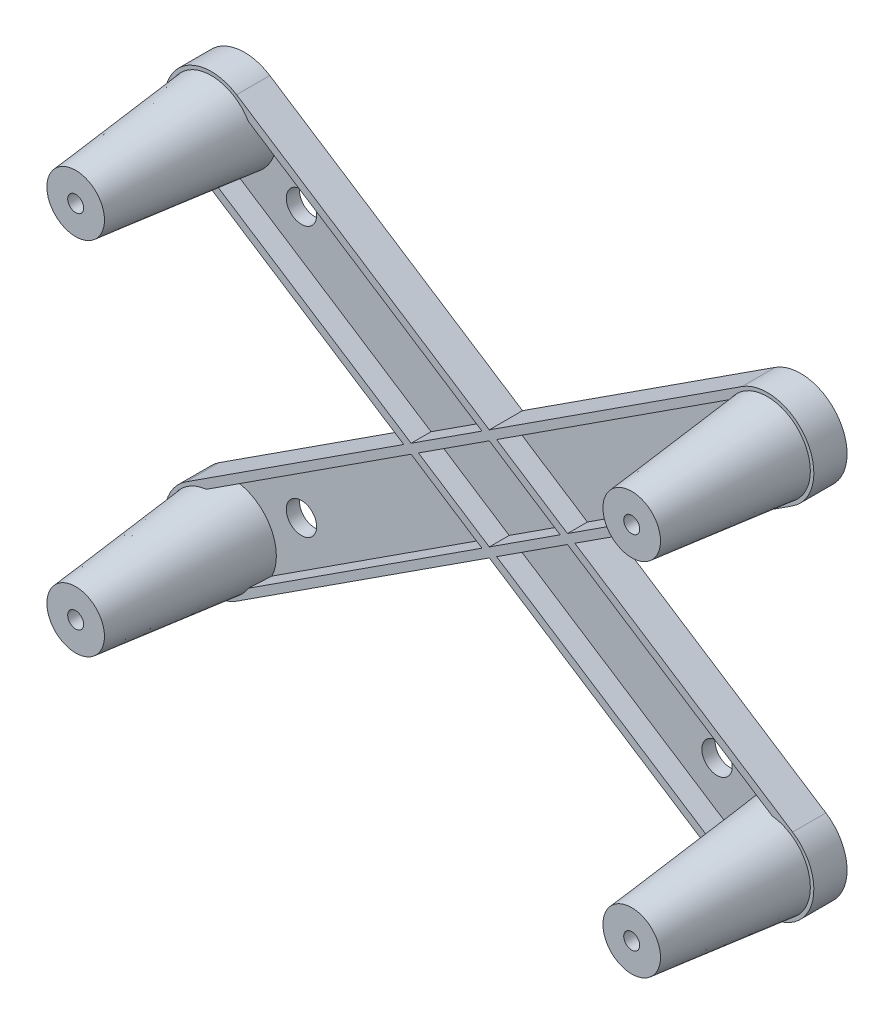
SolidWorks part; units mm, degrees
ref_plane "Front Plane" through (0, 0, 0) normal (0, 0, 1) x (1, 0, 0)
ref_plane "Top Plane" through (0, 0, 0) normal (0, 1, 0) x (1, 0, 0)
ref_plane "Right Plane" through (0, 0, 0) normal (1, 0, 0) x (0, 0, -1)
sketch "Guide Sketch" plane through (0, 0, 0) normal (0, 0, 1) x (1, 0, 0)
  circle A0 centre (0, 0) radius 1.75
  circle A1 centre (83.65, 0) radius 1.75
  circle A2 centre (83.65, 54.24) radius 1.75
  circle A3 centre (0, 54.24) radius 1.75
  dimension "D1" = 3.5
  dimension "D2" = 2
  dimension "D3" = 2
sketch "Sketch2" plane through (0, 0, 0) normal (0, 0, 1) x (1, 0, 0)
  line L0 (0, 54.24) -> (83.65, 0) construction
  line L1 (3.8084, 60.1134) -> (87.4584, 5.8734)
  line L2 (-3.8084, 48.3666) -> (79.8416, -5.8734)
  line L3 (83.65, 54.24) -> (0, 0) construction
  line L4 (87.4584, 48.3666) -> (3.8084, -5.8734)
  line L5 (79.8416, 60.1134) -> (-3.8084, 5.8734)
  line L6 (86.8055, 49.3735) -> (3.1555, -4.8665)
  line L7 (80.4945, 59.1065) -> (-3.1555, 4.8665)
  line L8 (3.1555, 59.1065) -> (86.8055, 4.8665)
  line L9 (-3.1555, 49.3735) -> (80.4945, -4.8665)
  arc A0 (3.8084, 60.1134) -> (-3.8084, 48.3666) centre (0, 54.24) ccw
  arc A1 (79.8416, -5.8734) -> (87.4584, 5.8734) centre (83.65, 0) ccw
  arc A2 (87.4584, 48.3666) -> (79.8416, 60.1134) centre (83.65, 54.24) ccw
  arc A3 (-3.8084, 5.8734) -> (3.8084, -5.8734) centre (0, 0) ccw
  arc A4 (-3.1555, 4.8665) -> (3.1555, -4.8665) centre (0, 0) ccw
  arc A5 (86.8055, 49.3735) -> (80.4945, 59.1065) centre (83.65, 54.24) ccw
  arc A6 (80.4945, -4.8665) -> (86.8055, 4.8665) centre (83.65, 0) ccw
  arc A7 (3.1555, 59.1065) -> (-3.1555, 49.3735) centre (0, 54.24) ccw
  point P4 (41.825, 27.12)
  point P9 (41.825, 27.12)
  dimension "D1" = 7
  dimension "D2" = 1.2
  dimension "D3" = 1.2
extrude "Base" add sketch "Sketch2" along normal blind 2 contours L4 A3 L5 A2 | L2 A1 L1 A0
sketch "Sketch3" plane through (0, 0, 0) normal (0, 0, 1) x (1, 0, 0)
  circle A0 centre (0, 54.24) radius 7
  circle A1 centre (0, 0) radius 7
  circle A2 centre (83.65, 0) radius 7
  circle A3 centre (83.65, 54.24) radius 7
extrude "Mounting Bosses" add sketch "Sketch3" along normal blind 25.4 draft 6
sketch "Sketch5" plane through (0, 0, 0) normal (0, 0, 1) x (1, 0, 0)
  line L0 (79.8416, 60.1134) -> (-3.8084, 5.8734) construction
  line L1 (80.4945, 59.1065) -> (-3.1555, 4.8665) construction
  line L2 (-3.8084, 48.3666) -> (79.8416, -5.8734) construction
  line L3 (-3.1555, 49.3735) -> (80.4945, -4.8665) construction
  line L4 (3.1555, 59.1065) -> (86.8055, 4.8665) construction
  line L5 (86.8055, 49.3735) -> (3.1555, -4.8665) construction
  line L6 (79.8416, 60.1134) -> (41.825, 35.4628)
  line L7 (80.4945, 59.1065) -> (42.9278, 34.7477)
  line L8 (-3.8084, 48.3666) -> (28.9586, 27.12)
  line L9 (-3.1555, 49.3735) -> (30.0615, 27.8351)
  line L10 (3.1555, 59.1065) -> (40.7222, 34.7477)
  line L11 (86.8055, 49.3735) -> (53.5885, 27.8351)
  line L12 (87.4584, 48.3666) -> (3.8084, -5.8734) construction
  line L13 (87.4584, 48.3666) -> (54.6914, 27.12)
  line L14 (30.0615, 26.4049) -> (40.7222, 19.4923)
  line L15 (31.1643, 27.12) -> (41.825, 20.2074)
  line L16 (28.9586, 27.12) -> (-3.8084, 5.8734)
  line L17 (30.0615, 26.4049) -> (-3.1555, 4.8665)
  line L18 (41.825, 18.7772) -> (79.8416, -5.8734)
  line L19 (42.9278, 19.4923) -> (80.4945, -4.8665)
  line L20 (41.825, 18.7772) -> (3.8084, -5.8734)
  line L21 (40.7222, 19.4923) -> (3.1555, -4.8665)
  line L22 (3.8084, 60.1134) -> (87.4584, 5.8734) construction
  line L23 (3.8084, 60.1134) -> (41.825, 35.4628)
  line L24 (41.825, 34.0326) -> (52.4857, 27.12)
  line L25 (42.9278, 34.7477) -> (53.5885, 27.8351)
  line L26 (40.7222, 34.7477) -> (30.0615, 27.8351)
  line L27 (41.825, 34.0326) -> (31.1643, 27.12)
  line L28 (53.5885, 26.4049) -> (42.9278, 19.4923)
  line L29 (52.4857, 27.12) -> (41.825, 20.2074)
  line L30 (53.5885, 26.4049) -> (86.8055, 4.8665)
  line L31 (54.6914, 27.12) -> (87.4584, 5.8734)
  arc A0 (3.1555, 59.1065) -> (-3.1555, 49.3735) centre (0, 54.24) ccw construction
  arc A1 (-3.1555, 4.8665) -> (3.1555, -4.8665) centre (0, 0) ccw construction
  arc A2 (80.4945, -4.8665) -> (86.8055, 4.8665) centre (83.65, 0) ccw construction
  arc A3 (3.1555, 59.1065) -> (-3.1555, 49.3735) centre (0, 54.24) ccw
  arc A4 (-3.1555, 4.8665) -> (3.1555, -4.8665) centre (0, 0) ccw
  arc A5 (80.4945, -4.8665) -> (86.8055, 4.8665) centre (83.65, 0) ccw
  arc A6 (-3.8084, 5.8734) -> (3.8084, -5.8734) centre (0, 0) ccw construction
  arc A7 (3.8084, 60.1134) -> (-3.8084, 48.3666) centre (0, 54.24) ccw construction
  arc A8 (-3.8084, 5.8734) -> (3.8084, -5.8734) centre (0, 0) ccw
  arc A9 (3.8084, 60.1134) -> (-3.8084, 48.3666) centre (0, 54.24) ccw
  arc A10 (87.4584, 48.3666) -> (79.8416, 60.1134) centre (83.65, 54.24) ccw construction
  arc A11 (79.8416, -5.8734) -> (87.4584, 5.8734) centre (83.65, 0) ccw construction
  arc A12 (87.4584, 48.3666) -> (79.8416, 60.1134) centre (83.65, 54.24) ccw
  arc A13 (79.8416, -5.8734) -> (87.4584, 5.8734) centre (83.65, 0) ccw
  arc A14 (86.8055, 49.3735) -> (80.4945, 59.1065) centre (83.65, 54.24) ccw construction
  arc A15 (86.8055, 49.3735) -> (80.4945, 59.1065) centre (83.65, 54.24) ccw
extrude "Ribw" add sketch "Sketch5" along normal blind 5
sketch "Sketch6" plane through (0, 0, 2) normal (0, 0, 1) x (1, 0, 0)
  circle A0 centre (10.5635, 6.8495) radius 5.8 construction
  circle A1 centre (10.5635, 47.3905) radius 5.8 construction
  circle A2 centre (73.3511, 47.562) radius 5.8 construction
  circle A3 centre (73.0865, 6.8495) radius 5.8 construction
  circle A4 centre (10.5635, 47.3905) radius 2.286
  circle A5 centre (10.5635, 6.8495) radius 2.286
  circle A6 centre (73.0865, 6.8495) radius 2.286
  circle A7 centre (73.3511, 47.562) radius 2.286
  dimension "D1" = 4.572
extrude "Mounting Holes" cut sketch "Sketch6" against normal through all contours A5 | A4 | A7 | A6
sketch "Sketch7" plane through (0, 0, 25.4) normal (0, 0, 1) x (1, 0, 0)
  circle A0 centre (0, 0) radius 1.2
  circle A1 centre (0, 54.24) radius 1.2
  circle A2 centre (83.65, 54.24) radius 1.2
  circle A3 centre (83.65, 0) radius 1.2
  dimension "D1" = 2.4
extrude "Screw Holes" cut sketch "Sketch7" against normal through all
